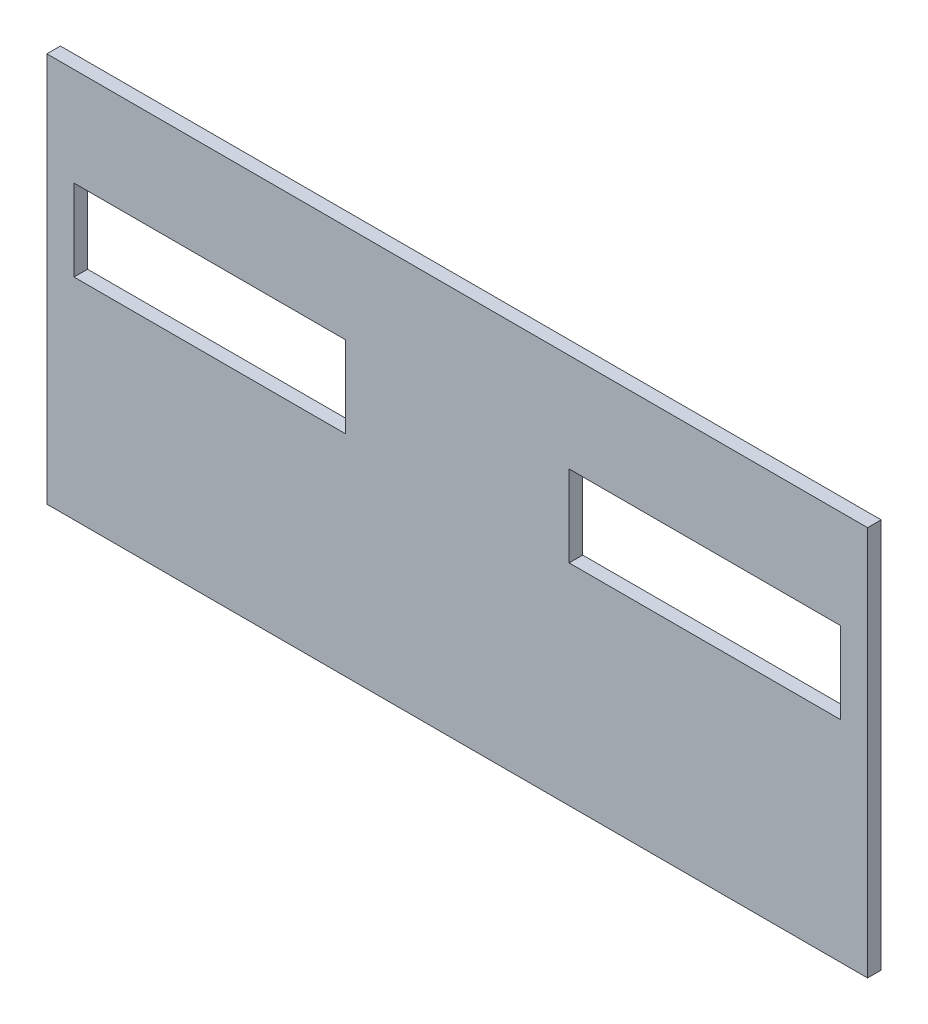
SolidWorks part; units mm, degrees
ref_plane "前视基准面" through (0, 0, 0) normal (0, 0, 1) x (1, 0, 0)
ref_plane "上视基准面" through (0, 0, 0) normal (0, 1, 0) x (1, 0, 0)
ref_plane "右视基准面" through (0, 0, 0) normal (1, 0, 0) x (0, 0, -1)
other "Configuration Table"
sketch "草图1" plane through (0, 0, 0) normal (0, 0, 1) x (1, 0, 0)
  line L1 (-99.0399, 66.2096) -> (142.9601, 66.2096)
  line L2 (-99.0399, 66.2096) -> (-99.0399, -48.7904)
  line L3 (-99.0399, -48.7904) -> (142.9601, -48.7904)
  line L4 (142.9601, 66.2096) -> (142.9601, -48.7904)
  line L5 (-91.0399, 37.2096) -> (-11.0399, 37.2096)
  line L6 (-91.0399, 37.2096) -> (-91.0399, 13.2096)
  line L7 (-91.0399, 13.2096) -> (-11.0399, 13.2096)
  line L8 (-11.0399, 37.2096) -> (-11.0399, 13.2096)
  line L9 (54.9601, 37.2096) -> (134.9601, 37.2096)
  line L10 (54.9601, 37.2096) -> (54.9601, 13.2096)
  line L11 (54.9601, 13.2096) -> (134.9601, 13.2096)
  line L12 (134.9601, 37.2096) -> (134.9601, 13.2096)
  dimension "D1" = 242
  dimension "D2" = 115
  dimension "D3" = 80
  dimension "D4" = 80
  dimension "D5" = 24
  dimension "D6" = 24
  dimension "D7" = 29
  dimension "D8" = 8
  dimension "D9" = 8
  dimension "D10" = 29
extrude "凸台-拉伸1" add sketch "草图1" along normal blind 4
